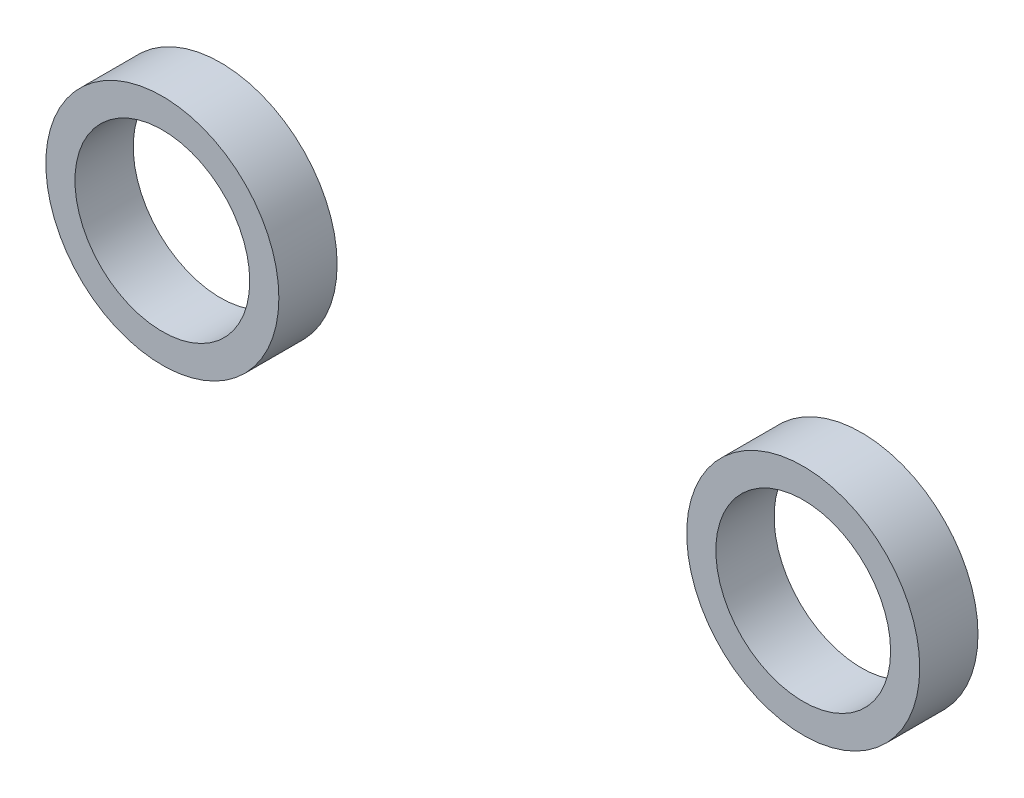
SolidWorks part; units mm, degrees
ref_plane "Front Plane" through (0, 0, 0) normal (0, 0, 1) x (1, 0, 0)
ref_plane "Top Plane" through (0, 0, 0) normal (0, 1, 0) x (1, 0, 0)
ref_plane "Right Plane" through (0, 0, 0) normal (1, 0, 0) x (0, 0, -1)
sketch "Sketch3" plane through (0, 0, 0) normal (0, 0, 1) x (1, 0, 0)
  circle A0 centre (33.2874, 165.1) radius 2.54
  circle A1 centre (47.2574, 165.1) radius 2.54
  circle A3 centre (33.2874, 165.1) radius 1.905
  circle A4 centre (47.2574, 165.1) radius 1.905
  dimension "D1" = 5.08
  dimension "D2" = 3.81
  dimension "D3" = 0.635
extrude "Boss-Extrude1" add sketch "Sketch3" along normal blind 1.27
